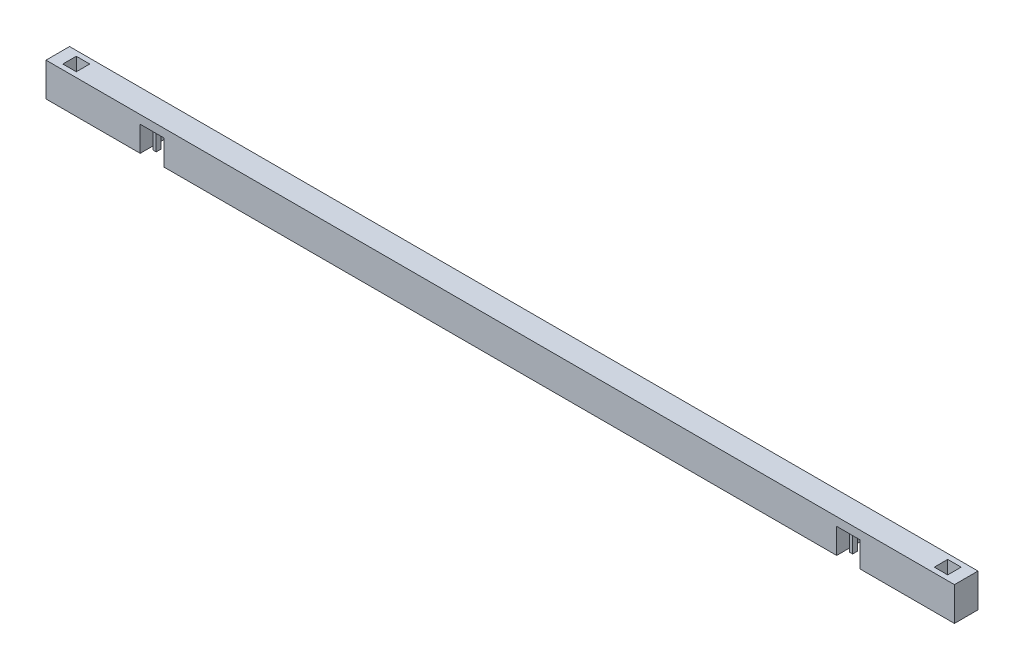
SolidWorks part; units mm, degrees
material "松木"
ref_plane "前视基准面" through (0, 0, 0) normal (0, 0, 1) x (1, 0, 0)
ref_plane "上视基准面" through (0, 0, 0) normal (0, 1, 0) x (1, 0, 0)
ref_plane "右视基准面" through (0, 0, 0) normal (1, 0, 0) x (0, 0, -1)
sketch "草图1" plane through (0, 0, 0) normal (0, 1, 0) x (1, 0, 0)
  line L1 (0, 0) -> (5400, 0)
  line L2 (0, 0) -> (0, 140)
  line L3 (0, 140) -> (5400, 140)
  line L4 (5400, 0) -> (5400, 140)
  dimension "D1" = 5400
  dimension "D2" = 140
extrude "凸台-拉伸1" add sketch "草图1" along normal blind 200
sketch "草图2" plane through (0, 0, 0) normal (0, -1, 0) x (1, 0, 0)
  line L0 (0, 0) -> (5400, 0) construction
  line L1 (580, -55) -> (600, -55)
  line L2 (580, -55) -> (580, -85)
  line L3 (580, -85) -> (600, -85)
  line L4 (600, -55) -> (600, -85)
  line L5 (0, -140) -> (0, 0) construction
  line L12 (660, -55) -> (680, -55)
  line L13 (660, -55) -> (660, -85)
  line L14 (660, -85) -> (680, -85)
  line L15 (680, -55) -> (680, -85)
  dimension "D1" = 20
  dimension "D2" = 30
  dimension "D3" = 55
  dimension "D4" = 580
  dimension "D5" = 20
  dimension "D6" = 30
  dimension "D7" = 660
extrude "凸台-拉伸2" add sketch "草图2" along normal blind 150
sketch "草图3" plane through (0, 0, 0) normal (0, -1, 0) x (1, 0, 0)
  line L0 (5400, -140) -> (0, -140) construction
  line L1 (560, -140) -> (700, -140)
  line L2 (560, -140) -> (560, 0)
  line L3 (560, 0) -> (700, 0)
  line L4 (700, -140) -> (700, 0)
  line L5 (0, 0) -> (5400, 0) construction
  line L6 (0, -140) -> (0, 0) construction
  line L7 (580, -85) -> (600, -85)
  line L8 (600, -85) -> (600, -55)
  line L9 (600, -55) -> (580, -55)
  line L10 (580, -55) -> (580, -85)
  line L11 (680, -85) -> (680, -55)
  line L12 (680, -55) -> (660, -55)
  line L13 (660, -55) -> (660, -85)
  line L14 (660, -85) -> (680, -85)
  dimension "D1" = 140
  dimension "D2" = 560
extrude "切除-拉伸1" cut sketch "草图3" against normal blind 150
sketch "草图4" plane through (0, 0, -140) normal (0, 0, -1) x (-1, 0, 0)
  line L0 (-5400, 0) -> (-700, 0) construction
  line L1 (-860, 0) -> (-560, 0)
  line L2 (-860, 0) -> (-860, -300)
  line L3 (-860, -300) -> (-560, -300)
  line L4 (-560, 0) -> (-560, -300)
  dimension "D1" = 300
  dimension "D2" = 300
  dimension "D3" = 560
extrude "切除-拉伸4" cut sketch "草图4" against normal through all
pattern_linear "阵列(线性)3" count 2 spacing 4140 along (1, 0, 0) of "切除-拉伸1"
sketch "草图5" plane through (0, 200, 0) normal (0, 1, 0) x (1, 0, 0)
  line L0 (5400, 0) -> (5400, 140) construction
  line L1 (5330, 110) -> (5250, 110)
  line L2 (5330, 110) -> (5330, 30)
  line L3 (5330, 30) -> (5250, 30)
  line L4 (5250, 110) -> (5250, 30)
  point P4 (5330, 70)
  point P7 (5400, 70)
  dimension "D1" = 80
  dimension "D2" = 80
  dimension "D3" = 70
extrude "切除-拉伸3" cut sketch "草图5" against normal blind 100
ref_plane "基准面1" through (2700, 0, 0) normal (1, 0, 0) x (0, 0, -1)
mirror "镜向1" about plane through (2700, 0, 0) normal (1, 0, 0) of "切除-拉伸3"
